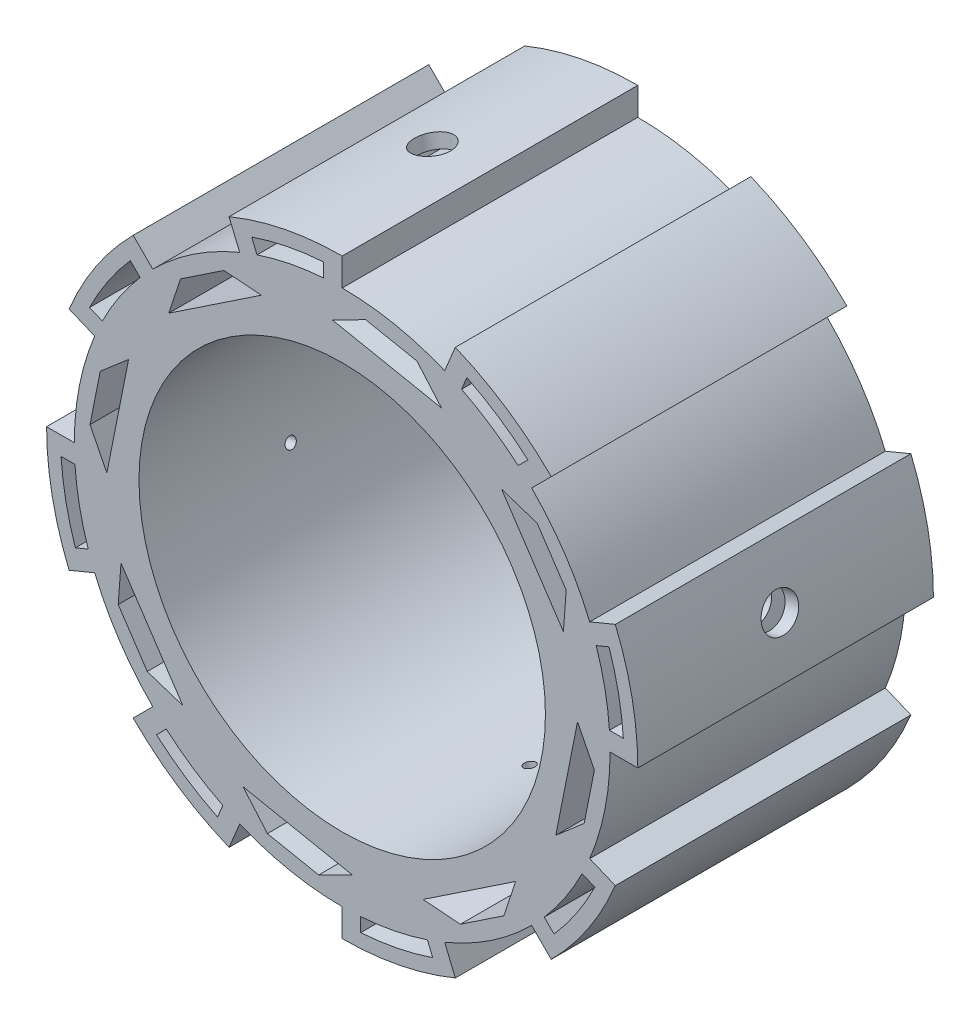
SolidWorks part; units mm, degrees
ref_plane "Front Plane" through (0, 0, 0) normal (0, 0, 1) x (1, 0, 0)
ref_plane "Top Plane" through (0, 0, 0) normal (0, 1, 0) x (1, 0, 0)
ref_plane "Right Plane" through (0, 0, 0) normal (1, 0, 0) x (0, 0, -1)
sketch "Base Drawing " plane through (0, 0, 0) normal (0, 0, 1) x (1, 0, 0)
  line L0 (0, 80) -> (0, -80)
  line L1 (-80, 0) -> (80, 0)
  line L2 (0, 0) -> (-56.5685, 56.5685)
  line L3 (-56.5685, 56.5685) -> (56.5685, -56.5685)
  line L4 (0, 0) -> (56.5685, 56.5685)
  line L5 (56.5685, 56.5685) -> (-56.5685, -56.5685)
  line L14 (0, 0) -> (-25.6326, 61.8826)
  line L15 (0, 0) -> (-30.6147, 73.9104)
  line L16 (-30.6147, 73.9104) -> (30.6147, -73.9104)
  line L17 (25.6326, 61.8826) -> (-25.6326, -61.8826)
  line L18 (-25.6326, -61.8826) -> (-30.6147, -73.9104)
  line L19 (-30.6147, -73.9104) -> (30.6147, 73.9104)
  line L20 (-61.8826, 25.6326) -> (73.9104, -30.6147)
  line L21 (73.9104, -30.6147) -> (-73.9104, 30.6147)
  line L22 (-61.8826, -25.6326) -> (73.9104, 30.6147)
  line L23 (73.9104, 30.6147) -> (-73.9104, -30.6147)
  arc A0 (0, 80) -> (-30.6147, 73.9104) centre (0, 0) ccw
  arc A1 (-27.7445, 66.9813) -> (-51.2652, 51.2652) centre (0, 0) ccw
  arc A2 (56.5685, 56.5685) -> (30.6147, 73.9104) centre (0, 0) ccw
  arc A3 (80, 0) -> (73.9104, 30.6147) centre (0, 0) ccw
  arc A4 (56.5685, -56.5685) -> (73.9104, -30.6147) centre (0, 0) ccw
  arc A5 (0, -80) -> (30.6147, -73.9104) centre (0, 0) ccw
  arc A6 (-56.5685, -56.5685) -> (-30.6147, -73.9104) centre (0, 0) ccw
  arc A7 (-80, 0) -> (-73.9104, -30.6147) centre (0, 0) ccw
  arc A8 (-56.5685, 56.5685) -> (-73.9104, 30.6147) centre (0, 0) ccw
  arc A9 (-66.9813, 27.7445) -> (-72.5, 0) centre (0, 0) ccw
  arc A10 (-66.9813, -27.7445) -> (-51.2652, -51.2652) centre (0, 0) ccw
  arc A11 (-27.7445, -66.9813) -> (0, -72.5) centre (0, 0) ccw
  arc A12 (27.7445, -66.9813) -> (51.2652, -51.2652) centre (0, 0) ccw
  arc A13 (66.9813, -27.7445) -> (72.5, 0) centre (0, 0) ccw
  arc A14 (66.9813, 27.7445) -> (51.2652, 51.2652) centre (0, 0) ccw
  arc A15 (27.7445, 66.9813) -> (0, 72.5) centre (0, 0) ccw
  dimension "D1" = 160
  dimension "D2" = 145
  dimension "D3" = 22.5
  dimension "D4" = 22.5
  dimension "D5" = 22.5
  dimension "D6" = 22.5
  dimension "D7" = 22.5
extrude "Boss-Extrude1" add sketch "Base Drawing " along normal blind 80 contours L0 A0 L16 L15 L14 | L15 A1 L2 L14 | L3 A8 L21 L20 L2 | L21 A9 L1 L20 | L1 A7 L23 L22 | L23 A10 L5 L22 | L5 A6 L19 L18 L17 | L18 A11 L0 L17 | L0 A5 L16 | L16 A12 L3 | L3 A4 L21 L20 | L20 A13 L1 | L1 A3 L23 L22 | L22 A14 L4 | L4 L5 A2 L19 L17 | L19 A15 L0 L17
sketch "Sketch2" plane through (0, 0, 80) normal (0, 0, 1) x (1, 0, 0)
  circle A0 centre (0, 0) radius 55
  dimension "D1" = 110
extrude "Cut-Extrude1" cut sketch "Sketch2" against normal blind 127 and the other way blind 67
sketch "Sketch3" plane through (0, 0, 0) normal (0, 0, -1) x (-1, 0, 0)
  line L0 (51.2652, 51.2652) -> (56.5685, 56.5685)
  line L1 (-53.033, 60.1041) -> (-47.6076, 54.6787)
  line L2 (-51.2652, 51.2652) -> (-56.5685, 56.5685)
  line L3 (-35.2341, 71.9969) -> (-32.3639, 65.0678)
  line L4 (-51.2652, 51.2652) -> (-47.7297, 54.8008)
  line L5 (-56.5685, 56.5685) -> (-53.033, 60.1041)
  line L6 (-47.7297, 54.8008) -> (-53.033, 60.1041)
  line L7 (-27.7445, 66.9813) -> (-30.6147, 73.9104)
  line L8 (-27.7445, 66.9813) -> (-32.3639, 65.0678)
  line L9 (-30.6147, 73.9104) -> (-35.2341, 71.9969)
  line L10 (-32.3639, 65.0678) -> (-35.2341, 71.9969)
  line L11 (-35.2341, 71.9969) -> (-32.2979, 64.9084)
  line L12 (-66.9813, 27.7445) -> (-73.9104, 30.6147)
  line L13 (-66.9813, 27.7445) -> (-68.8947, 23.1252)
  line L14 (-73.9104, 30.6147) -> (-75.8238, 25.9953)
  line L15 (-68.8947, 23.1252) -> (-75.8238, 25.9953)
  line L16 (-72.5, 0) -> (-80, 0)
  line L17 (-72.5, 0) -> (-72.5, 5)
  line L18 (-80, 0) -> (-80, 5)
  line L19 (-72.5, 5) -> (-80, 5)
  line L20 (-75.8238, 25.9953) -> (-68.8947, 23.1252)
  line L21 (-75.8238, 25.9953) -> (-68.7352, 23.0591)
  line L25 (-80, 5) -> (-72.3274, 5)
  line L29 (-66.9813, -27.7445) -> (-73.9104, -30.6147)
  line L30 (-66.9813, -27.7445) -> (-65.0678, -32.3639)
  line L31 (-73.9104, -30.6147) -> (-71.9969, -35.2341)
  line L32 (-65.0678, -32.3639) -> (-71.9969, -35.2341)
  line L33 (-51.2652, -51.2652) -> (-56.5685, -56.5685)
  line L34 (-51.2652, -51.2652) -> (-54.8008, -47.7297)
  line L35 (-56.5685, -56.5685) -> (-60.1041, -53.033)
  line L36 (-54.8008, -47.7297) -> (-60.1041, -53.033)
  line L37 (-60.1041, -53.033) -> (-54.6787, -47.6076)
  line L41 (-68.3635, -33.7291) -> (-64.9084, -32.2979)
  line L45 (-30.6147, -73.9104) -> (-27.7445, -66.9813)
  line L46 (-30.6147, -73.9104) -> (-25.9953, -75.8238)
  line L47 (-27.7445, -66.9813) -> (-23.1252, -68.8947)
  line L48 (-25.9953, -75.8238) -> (-23.1252, -68.8947)
  line L49 (0, -72.5) -> (0, -80)
  line L50 (0, -72.5) -> (-5, -72.5)
  line L51 (0, -80) -> (-5, -80)
  line L52 (-5, -72.5) -> (-5, -80)
  line L53 (-24.4179, -72.0157) -> (-23.0591, -68.7352)
  line L57 (-5, -75.3651) -> (-5, -72.3274)
  line L61 (51.2652, -51.2652) -> (56.5685, -56.5685)
  line L62 (51.2652, -51.2652) -> (47.7297, -54.8008)
  line L63 (56.5685, -56.5685) -> (53.033, -60.1041)
  line L64 (47.7297, -54.8008) -> (53.033, -60.1041)
  line L65 (51.2652, -51.2652) -> (56.5685, -56.5685) construction
  line L66 (27.7445, -66.9813) -> (30.6147, -73.9104)
  line L67 (27.7445, -66.9813) -> (32.3639, -65.0678)
  line L68 (30.6147, -73.9104) -> (35.2341, -71.9969)
  line L69 (32.3639, -65.0678) -> (35.2341, -71.9969)
  line L70 (27.7445, -66.9813) -> (30.6147, -73.9104) construction
  line L71 (33.6039, -68.0615) -> (32.2979, -64.9084)
  line L75 (50.2653, -57.3364) -> (47.6076, -54.6787)
  line L79 (72.5, 0) -> (80, 0)
  line L80 (72.5, 0) -> (72.5, -5)
  line L81 (80, 0) -> (80, -5)
  line L82 (72.5, -5) -> (80, -5)
  line L83 (66.9813, -27.7445) -> (73.9104, -30.6147)
  line L84 (66.9813, -27.7445) -> (68.8947, -23.1252)
  line L85 (73.9104, -30.6147) -> (75.8238, -25.9953)
  line L86 (68.8947, -23.1252) -> (75.8238, -25.9953)
  line L87 (75.8238, -5) -> (72.3274, -5)
  line L91 (70.3826, -23.7415) -> (68.7352, -23.0591)
  line L95 (51.2652, 51.2652) -> (56.5685, 56.5685)
  line L96 (51.2652, 51.2652) -> (54.8008, 47.7297)
  line L97 (56.5685, 56.5685) -> (60.1041, 53.033)
  line L98 (54.8008, 47.7297) -> (60.1041, 53.033)
  line L99 (66.9813, 27.7445) -> (73.9104, 30.6147)
  line L100 (66.9813, 27.7445) -> (65.0678, 32.3639)
  line L101 (73.9104, 30.6147) -> (71.9969, 35.2341)
  line L102 (65.0678, 32.3639) -> (71.9969, 35.2341)
  line L103 (56.1843, 49.1133) -> (54.6787, 47.6076)
  line L115 (66.3364, 32.8894) -> (64.9084, 32.2979)
  line L119 (54.68, 47.6089) -> (54.6774, 47.6063)
  line L120 (65.4316, 32.5146) -> (64.8373, 32.2685)
  line L121 (72.3373, -5) -> (72.3238, -5)
  line L122 (69.253, -23.2736) -> (67.2291, -22.4352)
  line L123 (48.4708, -55.5419) -> (44.4221, -51.4932)
  line L124 (32.9362, -66.4493) -> (30.6147, -60.923)
  line L125 (-5, -74.4641) -> (-5, -60.1041)
  line L126 (-23.9325, -70.8438) -> (-18.526, -57.7914)
  line L127 (-56.2569, -49.1859) -> (-52.4574, -45.3864)
  line L128 (-66.9813, -33.1565) -> (-57.4433, -29.2057)
  line L129 (-74.6687, 5) -> (-65.0678, 5)
  line L130 (-71.0014, 23.9978) -> (-65.0678, 21.54)
  line L131 (-49.2038, 56.2749) -> (-44.0713, 51.1424)
  line L132 (-33.1565, 66.9813) -> (-30.6147, 60.8447)
  line L133 (0, 72.5) -> (0, 80)
  line L134 (0, 72.5) -> (5, 72.5)
  line L135 (0, 80) -> (5, 80)
  line L136 (5, 72.5) -> (5, 80)
  line L137 (27.7445, 66.9813) -> (30.6147, 73.9104)
  line L138 (27.7445, 66.9813) -> (23.1252, 68.8947)
  line L139 (30.6147, 73.9104) -> (25.9953, 75.8238)
  line L140 (23.1252, 68.8947) -> (25.9953, 75.8238)
  line L141 (5, 74.9522) -> (5, 69.1426)
  line L142 (24.1329, 71.3276) -> (21.7386, 65.5472)
  circle A0 centre (0, 0) radius 72.5
  arc A1 (30.6147, -73.9104) -> (56.5685, -56.5685) centre (0, 0) ccw construction
  circle A2 centre (0, 0) radius 76.25
  dimension "D1" = 152.5
  dimension "D2" = 5
  dimension "D3" = 5
  dimension "D4" = 5
  dimension "D5" = 5
  dimension "D6" = 5
  dimension "D7" = 5
  dimension "D8" = 5
  dimension "D9" = 5
  dimension "D10" = 5
  dimension "D11" = 5
  dimension "D12" = 5
  dimension "D13" = 5
  dimension "D14" = 5
  dimension "D15" = 5
  dimension "D16" = 5
  dimension "D17" = 5
extrude "Cut-Extrude2" cut sketch "Sketch3" against normal blind 103 and the other way blind 21 contours L11 A2 L6 L1 A0 | L21 A2 L25 L19 A0 L15 | L32 A2 L37 L36 A0 L41 | L48 A2 L52 L57 A0 L53 | L69 A2 L75 L64 A0 L71 | L86 A2 L82 L87 A0 L91 | L102 A2 L98 L103 A0 L115 | L140 A2 L136 L141 A0 L142
sketch "Sketch5" plane through (0, 0, 0) normal (0, 0, -1) x (-1, 0, 0)
  line L0 (-27.7445, 66.9813) -> (51.2652, 51.2652)
  line L1 (66.9813, 27.7445) -> (51.2652, -51.2652)
  line L2 (27.7445, -66.9813) -> (-51.2652, -51.2652)
  line L3 (-66.9813, -27.7445) -> (-51.2652, 51.2652)
  line L4 (27.7445, 66.9813) -> (72.5, 0)
  line L5 (66.9813, -27.7445) -> (0, -72.5)
  line L6 (-27.7445, -66.9813) -> (-72.5, 0)
  line L7 (-66.9813, 27.7445) -> (0, 72.5)
  line L8 (-66.9813, 27.7445) -> (-72.5, 0)
  line L9 (-51.2652, 51.2652) -> (-27.7445, 66.9813)
  line L10 (0, 72.5) -> (27.7445, 66.9813)
  line L11 (51.2652, 51.2652) -> (66.9813, 27.7445)
  line L12 (72.5, 0) -> (66.9813, -27.7445)
  line L13 (51.2652, -51.2652) -> (27.7445, -66.9813)
  line L14 (0, -72.5) -> (-27.7445, -66.9813)
  line L15 (-51.2652, -51.2652) -> (-66.9813, -27.7445)
  line L16 (-27.7445, 66.9813) -> (0, 72.5)
  line L17 (27.7445, 66.9813) -> (51.2652, 51.2652)
  line L18 (66.9813, 27.7445) -> (72.5, 0)
  line L19 (66.9813, -27.7445) -> (51.2652, -51.2652)
  line L20 (27.7445, -66.9813) -> (0, -72.5)
  line L21 (-27.7445, -66.9813) -> (-51.2652, -51.2652)
  line L22 (-66.9813, -27.7445) -> (-72.5, 0)
  line L23 (-66.9813, 27.7445) -> (-51.2652, 51.2652)
  line L24 (-27.7445, 66.9813) -> (-12.7293, 63.9945)
  line L25 (-12.7293, 63.9945) -> (-20.2369, 65.4879)
  line L26 (-20.2369, 65.4879) -> (-33.4906, 50.1223)
  line L27 (-12.7293, 63.9945) -> (0, 72.5)
  line L28 (-6.3647, 68.2473) -> (11.7603, 59.1233)
  line L29 (-20.2369, 65.4879) -> (-6.3647, 68.2473)
  line L30 (-26.8638, 57.8051) -> (2.6978, 63.6853)
  line L31 (-66.9813, 27.7445) -> (-54.252, 36.25)
  line L32 (-54.252, 36.25) -> (-51.2652, 51.2652)
  line L33 (-52.7586, 43.7576) -> (-33.4906, 50.1223)
  line L34 (-66.9813, 27.7445) -> (-54.252, 36.25)
  line L35 (-60.6166, 31.9973) -> (-59.1233, 11.7603)
  line L36 (-60.6166, 31.9973) -> (-52.7586, 43.7576)
  line L38 (-59.8699, 21.8788) -> (-43.1246, 46.9399)
  line L39 (-72.5, 0) -> (-63.9945, -12.7293)
  line L40 (-63.9945, -12.7293) -> (-66.9813, -27.7445)
  line L41 (-68.2473, -6.3647) -> (-59.1233, 11.7603)
  line L42 (-66.9813, -27.7445) -> (-63.9945, -12.7293)
  line L43 (-65.4879, -20.2369) -> (-50.1223, -33.4906)
  line L45 (-68.2473, -6.3647) -> (-65.4879, -20.2369)
  line L46 (-63.9945, -12.7293) -> (-59.1233, 11.7603)
  line L47 (-63.6853, 2.6978) -> (-57.8051, -26.8638)
  line L48 (34.4094, 51.4973) -> (39.5049, 59.1233)
  line L49 (39.5049, 59.1233) -> (36.25, 54.252)
  line L50 (36.25, 54.252) -> (27.7445, 66.9813)
  line L51 (36.25, 54.252) -> (51.2652, 51.2652)
  line L52 (43.7576, 52.7586) -> (31.9973, 60.6166)
  line L53 (31.9973, 60.6166) -> (11.7603, 59.1233)
  line L54 (43.7576, 52.7586) -> (50.1223, 33.4906)
  line L55 (46.9399, 43.1246) -> (21.8788, 59.8699)
  line L56 (69.7406, 13.8723) -> (63.9945, 12.7293)
  line L57 (63.9945, 12.7293) -> (66.9813, 27.7445)
  line L58 (63.9945, 12.7293) -> (72.5, 0)
  line L59 (68.2473, 6.3647) -> (65.4879, 20.2369)
  line L60 (65.4879, 20.2369) -> (50.1223, 33.4906)
  line L61 (68.2473, 6.3647) -> (59.1233, -11.7603)
  line L62 (63.6853, -2.6978) -> (57.8051, 26.8638)
  line L63 (59.1233, -39.5049) -> (54.252, -36.25)
  line L64 (54.252, -36.25) -> (66.9813, -27.7445)
  line L65 (54.252, -36.25) -> (51.2652, -51.2652)
  line L66 (52.7586, -43.7576) -> (60.6166, -31.9973)
  line L67 (60.6166, -31.9973) -> (59.1233, -11.7603)
  line L68 (52.7586, -43.7576) -> (33.4906, -50.1223)
  line L69 (43.1246, -46.9399) -> (59.8699, -21.8788)
  line L70 (13.8723, -69.7406) -> (12.7293, -63.9945)
  line L71 (0, -72.5) -> (12.7293, -63.9945)
  line L72 (27.7445, -66.9813) -> (12.7293, -63.9945)
  line L73 (6.3647, -68.2473) -> (20.2369, -65.4879)
  line L74 (20.2369, -65.4879) -> (33.4906, -50.1223)
  line L75 (6.3647, -68.2473) -> (-11.7603, -59.1233)
  line L76 (-2.6978, -63.6853) -> (26.8638, -57.8051)
  line L77 (-39.5049, -59.1233) -> (-36.25, -54.252)
  line L78 (-51.2652, -51.2652) -> (-36.25, -54.252)
  line L79 (-27.7445, -66.9813) -> (-36.25, -54.252)
  line L80 (-43.7576, -52.7586) -> (-50.1223, -33.4906)
  line L81 (-31.9973, -60.6166) -> (-11.7603, -59.1233)
  line L82 (-43.7576, -52.7586) -> (-31.9973, -60.6166)
  line L83 (-21.8788, -59.8699) -> (-46.9399, -43.1246)
extrude "Cut-Extrude3" cut sketch "Sketch5" against normal blind 105 and the other way blind 36 contours L35 L38 L3 L34 | L3 L38 L7 | L7 L38 L33 L3 | L36 L34 L3 | L26 L30 L7 L24 | L29 L24 L7 | L0 L30 L28 L7 | L7 L30 L0 | L55 L0 L50 L53 | L55 L48 L0 | L55 L54 L0 L4 | L0 L52 L48 | L48 L52 L50 | L55 L4 L48 | L62 L61 L4 L1 | L62 L1 L4 | L62 L4 L57 L60 | L56 L59 L57 | L4 L59 L56 | L1 L66 L63 | L63 L66 L64 | L69 L1 L64 L67 | L69 L5 L1 | L69 L68 L1 L5 | L76 L75 L5 L2 | L5 L73 L70 | L70 L73 L72 | L76 L5 L72 L74 | L76 L2 L5 | L6 L83 L80 L2 | L2 L82 L77 | L77 L82 L79 | L81 L83 L2 L79 | L2 L83 L6 | L47 L41 L6 L3 | L6 L45 L42 | L47 L6 L42 L43 | L47 L3 L6
ref_plane "Plane8" through (80, 0, 0) normal (1, 0, 0) x (0, 0, -1)
ref_plane "Plane9" through (78.4628, 15.6072, 0) normal (0.9808, 0.1951, 0) x (0, 0, -1)
sketch "Sketch14" plane through (78.4628, 15.6072, 0) normal (0.9808, 0.1951, 0) x (0, 0, -1)
  line L0 (0, 0) -> (-80, 0)
  circle A0 centre (-40, 0) radius 5
  dimension "D2" = 10
  dimension "D1" = 80
extrude "Cut-Extrude4" cut sketch "Sketch14" against normal blind 15 contours L0 A0 | L0 A0
ref_plane "Plane10" through (-80, 0, 0) normal (1, 0, 0) x (0, 0, -1)
ref_plane "Plane11" through (-78.4628, -15.6072, 0) normal (-0.9808, -0.1951, 0) x (0, 0, -1)
sketch "Sketch15" plane through (-78.4628, -15.6072, 0) normal (-0.9808, -0.1951, 0) x (0, 0, -1)
  line L0 (0, 0) -> (-80, 0)
  line L1 (-80, 15.6072) -> (-80, -15.6072) construction
  circle A0 centre (-40, 0) radius 5
  dimension "D1" = 10
extrude "Cut-Extrude5" cut sketch "Sketch15" against normal blind 15 contours L0 A0 | L0 A0
sketch "Test " plane through (0, 0, 0) normal (0, 0, -1) x (-1, 0, 0)
  line L0 (-36.1121, 54.0455) -> (-36.0799, 53.9974)
  line L1 (54.6787, 47.6076) -> (57.4801, 43.9432)
  line L2 (-47.6076, 54.6787) -> (-43.7802, 57.2361)
  line L3 (-47.6076, 54.6787) -> (-43.3427, 48.2958)
  line L5 (-19.0191, 59.3655) -> (-18.9401, 58.9682)
  line L6 (-32.2979, 64.9084) -> (-28.033, 58.5255)
  line L7 (-43.3427, 48.2958) -> (-28.033, 58.5255)
  line L8 (32.2979, -64.9084) -> (36.1253, -62.351)
  line L9 (32.2979, -64.9084) -> (28.0164, -58.5006)
  line L10 (47.6076, -54.6787) -> (43.3261, -48.271)
  line L11 (28.0164, -58.5006) -> (43.3261, -48.271)
  line L12 (64.9084, 32.2979) -> (62.351, 36.1253)
  line L13 (64.9084, 32.2979) -> (58.6137, 28.0919)
  line L14 (54.6787, 47.6076) -> (48.384, 43.4017)
  line L15 (58.6137, 28.0919) -> (48.384, 43.4017)
  line L16 (-54.6787, -47.6076) -> (-57.2361, -43.7802)
  line L17 (-54.6787, -47.6076) -> (-48.3825, -43.4007)
  line L18 (-64.9084, -32.2979) -> (-58.6122, -28.0909)
  line L19 (-48.3825, -43.4007) -> (-58.6122, -28.0909)
  line L20 (-47.6076, 54.6787) -> (-43.9432, 57.4801)
  line L21 (-36.2884, 62.595) -> (-32.2979, 64.9084)
  line L22 (-36.1253, 62.351) -> (-32.2979, 64.9084)
  line L24 (-43.9432, 57.4801) -> (-39.9073, 51.4399)
  line L25 (-36.2884, 62.595) -> (-32.2524, 56.5548)
  line L28 (-43.9432, 57.4801) -> (-48.5514, 64.3768)
  line L29 (-36.2884, 62.595) -> (-40.8966, 69.4916)
  line L30 (-48.5514, 64.3768) -> (-40.8966, 69.4916)
  line L31 (-39.9073, 51.4399) -> (-39.5153, 50.8532)
  line L32 (-32.2524, 56.5548) -> (-31.8604, 55.968)
  line L34 (36.2817, -62.5849) -> (32.194, -56.4672)
  line L36 (32.194, -56.4672) -> (42.0677, -71.2443)
  line L37 (39.8488, -51.3524) -> (49.7226, -66.1295)
  line L38 (42.0677, -71.2443) -> (49.7226, -66.1295)
  line L39 (39.9528, -59.7935) -> (40.2788, -60.2815)
  line L40 (43.7802, -57.2361) -> (47.6076, -54.6787)
  line L41 (-64.9084, -32.2979) -> (-62.595, -36.2884)
  line L42 (-57.4801, -43.9432) -> (-54.6787, -47.6076)
  line L43 (-62.595, -36.2884) -> (-56.4672, -32.194)
  line L44 (-57.4801, -43.9432) -> (-51.3524, -39.8488)
  line L45 (-56.4672, -32.194) -> (-51.3524, -39.8488)
  line L46 (-56.4672, -32.194) -> (-71.7178, -42.384)
  line L47 (-51.3524, -39.8488) -> (-66.6029, -50.0389)
  line L48 (-71.7178, -42.384) -> (-66.6029, -50.0389)
  line L49 (-53.9098, -36.0214) -> (-53.4973, -35.7458)
  line L50 (-62.351, -36.1253) -> (-64.9084, -32.2979)
  line L51 (62.595, 36.2884) -> (64.9084, 32.2979)
  line L52 (57.4801, 43.9432) -> (51.3524, 39.8488)
  line L53 (62.595, 36.2884) -> (56.4672, 32.194)
  line L54 (57.4801, 43.9432) -> (51.3524, 39.8488)
  line L55 (62.595, 36.2884) -> (56.4672, 32.194)
  line L56 (51.3524, 39.8488) -> (56.4672, 32.194)
  line L57 (51.3524, 39.8488) -> (66.7151, 50.1139)
  line L58 (56.4672, 32.194) -> (71.83, 42.459)
  line L59 (66.7151, 50.1139) -> (71.83, 42.459)
  line L60 (39.4987, -50.8284) -> (48.1994, -63.8499)
  line L61 (57.2361, 43.7802) -> (54.6787, 47.6076)
  line L62 (31.8438, -55.9432) -> (40.5445, -68.9648)
  line L63 (53.4989, 35.7468) -> (54.0455, 36.1121)
  arc A1 (30.6147, -73.9104) -> (56.5685, -56.5685) centre (0, 0) ccw construction
  arc A2 (-39.8488, 51.3524) -> (-43.4029, 48.3858) centre (0, 0) ccw
  arc A3 (39.8488, -51.3524) -> (43.4029, -48.3858) centre (0, 0) ccw
  arc A4 (32.2979, -64.9084) -> (47.6076, -54.6787) centre (0, 0) ccw construction
  arc A5 (-58.6155, -28.0931) -> (-56.4672, -32.194) centre (0, 0) ccw
  arc A7 (-51.3524, -39.8488) -> (32.194, -56.4672) centre (0, 0) ccw
  arc A8 (-28.0931, 58.6155) -> (-32.194, 56.4672) centre (0, 0) ccw
  arc A9 (58.6155, 28.0931) -> (48.3858, 43.4029) centre (0, 0) ccw
  dimension "D1" = 130
  dimension "D2" = 9.2064
  dimension "D3" = 9.2064
ref_plane "Plane13" through (0, 80, 0) normal (0, 1, 0) x (1, 0, 0)
ref_plane "Plane14" through (-15.6072, 78.4628, 0) normal (-0.1951, 0.9808, 0) x (0, 0, -1)
sketch "Sketch16" plane through (-15.6072, 78.4628, 0) normal (-0.1951, 0.9808, 0) x (0, 0, -1)
  line L0 (0, 0) -> (-80, 0)
  line L1 (0, -42.5916) -> (0, 42.5916) construction
  line L2 (-80, 15.6072) -> (-80, -15.6072) construction
  circle A0 centre (-40, 0) radius 5
  dimension "D1" = 10
extrude "Cut-Extrude6" cut sketch "Sketch16" against normal blind 15 contours L0 A0 | L0 A0
ref_plane "Plane15" through (15.6072, -78.4628, 0) normal (0.1951, -0.9808, 0) x (0, 0, -1)
sketch "Sketch17" plane through (15.6072, -78.4628, 0) normal (0.1951, -0.9808, 0) x (0, 0, -1)
  line L0 (0, 0) -> (-80, 0)
  circle A0 centre (-40, 0) radius 5
  dimension "D2" = 10
  dimension "D1" = 80
extrude "Cut-Extrude7" cut sketch "Sketch17" against normal blind 15 contours L0 A0 | L0 A0
sketch "Sketch18" plane through (78.4628, 15.6072, 0) normal (0.9808, 0.1951, 0) x (0, 0, -1)
  line L0 (-45, 0) -> (-41.5, 0)
  circle A0 centre (-40, 0) radius 5 construction
  circle A1 centre (-40, 0) radius 5 construction
  circle A2 centre (-40, 0) radius 1.5
  dimension "D1" = 3
extrude "M3 Hole1" cut sketch "Sketch18" against normal blind 190 contours A2
sketch "Sketch19" plane through (-15.6072, 78.4628, 0) normal (-0.1951, 0.9808, 0) x (0, 0, -1)
  circle A0 centre (-40, 0) radius 1.5
  dimension "D1" = 3
extrude "M3 Hole2" cut sketch "Sketch19" against normal blind 190
